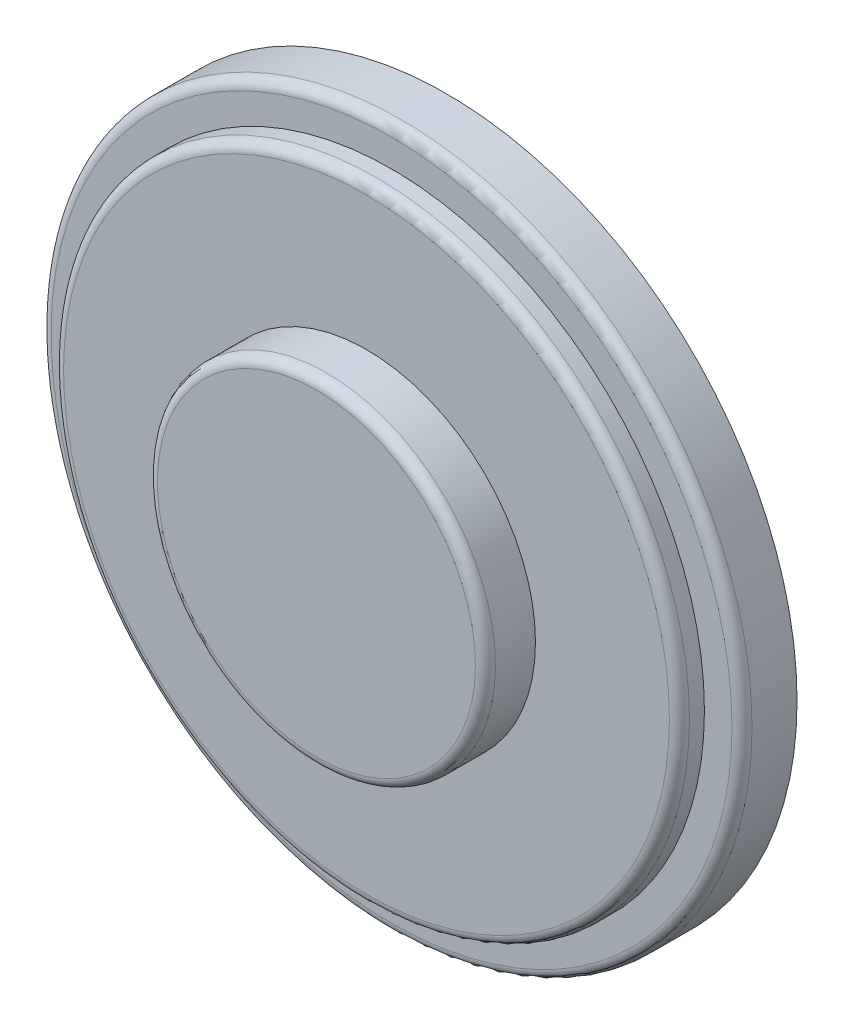
SolidWorks part; units mm, degrees
ref_plane "Front Plane" through (0, 0, 0) normal (0, 0, 1) x (1, 0, 0)
ref_plane "Top Plane" through (0, 0, 0) normal (0, 1, 0) x (1, 0, 0)
ref_plane "Right Plane" through (0, 0, 0) normal (1, 0, 0) x (0, 0, -1)
sketch "Sketch2" plane through (0, 0, 0) normal (0, 0, 1) x (1, 0, 0)
  circle A0 centre (0, 0) radius 14
  dimension "D1" = 28
extrude "Boss-Extrude2" add sketch "Sketch2" along normal blind 2.2
sketch "Sketch3" plane through (0, 0, 0) normal (0, 0, 1) x (1, 0, 0)
  circle A0 centre (0, 0) radius 12.5
extrude "Boss-Extrude5" add sketch "Sketch3" along normal blind 3.2
sketch "Sketch4" plane through (0, 0, 0) normal (0, 0, 1) x (1, 0, 0)
  circle A0 centre (0, 0) radius 6.75
extrude "Boss-Extrude6" add sketch "Sketch4" along normal blind 5.2
fillet "Fillet1" radius 0.4 3 edges at (14, 0, 2.2) (12.5, 0, 3.2) (6.75, 0, 5.2)
